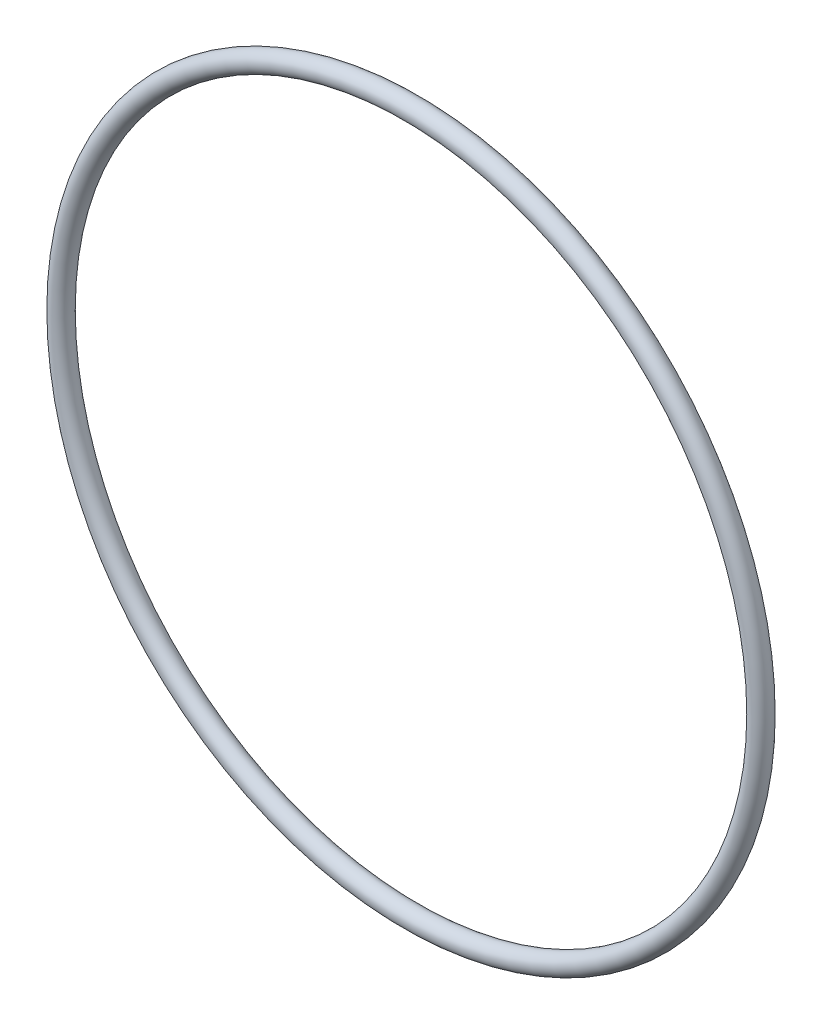
SolidWorks part; units mm, degrees
ref_plane "Front Plane" through (0, 0, 0) normal (0, 0, 1) x (1, 0, 0)
ref_plane "Top Plane" through (0, 0, 0) normal (0, 1, 0) x (1, 0, 0)
ref_plane "Right Plane" through (0, 0, 0) normal (1, 0, 0) x (0, 0, -1)
sketch "Sketch-path" plane through (0, 0, 0) normal (0, 0, 1) x (1, 0, 0)
  circle A0 centre (0, 0) radius 55.245
  dimension "D1" = 110.49
sweep "Base-Sweep" add path "Sketch-path" circular profile diameter 3.175 parameters "D3"=3.175
